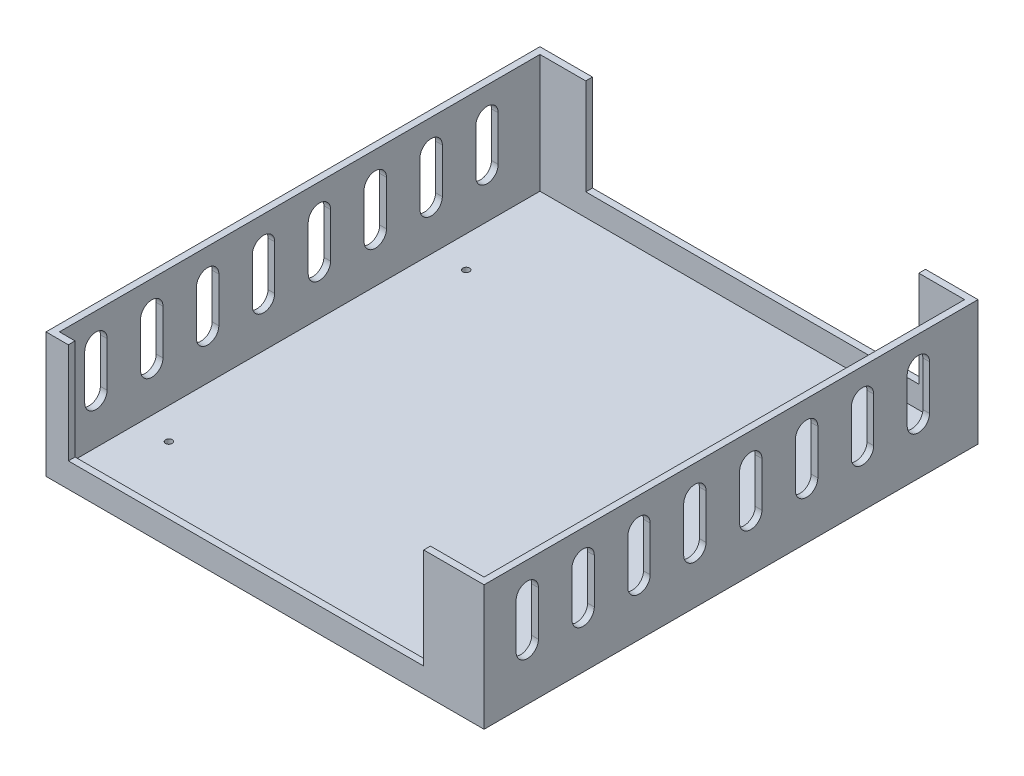
SolidWorks part; units mm, degrees
ref_plane "前视基准面" through (0, 0, 0) normal (0, 0, 1) x (1, 0, 0)
ref_plane "上视基准面" through (0, 0, 0) normal (0, 1, 0) x (1, 0, 0)
ref_plane "右视基准面" through (0, 0, 0) normal (1, 0, 0) x (0, 0, -1)
sketch "草图1" plane through (0, 0, 0) normal (0, 1, 0) x (1, 0, 0)
  line L0 (0, 0) -> (190, 0)
  line L1 (0, 0) -> (0, 215)
  line L2 (0, 215) -> (190, 215)
  line L3 (190, 215) -> (190, 0)
  line L4 (190, 0) -> (190, 11)
  line L5 (-3, -3) -> (193, -3)
  line L6 (-3, -3) -> (-3, 218)
  line L7 (-3, 218) -> (193, 218)
  line L8 (193, 218) -> (193, -3)
  circle A4 centre (14, 168) radius 1.5
  circle A5 centre (173, 168) radius 1.5
  circle A6 centre (173, 11) radius 1.5
  circle A7 centre (14, 35) radius 1.5
  dimension "D1" = 3
ref_plane "基准面1" through (0, -3, 0) normal (0, 1, 0) x (1, 0, 0)
sketch "草图2" plane through (0, -3, 0) normal (0, 1, 0) x (1, 0, 0)
  line L0 (-3, 218) -> (193, 218)
  line L1 (193, 218) -> (193, -3)
  line L2 (193, -3) -> (-3, -3)
  line L3 (-3, -3) -> (-3, 218)
  circle A0 centre (14, 168) radius 1.5
  circle A1 centre (173, 168) radius 1.5
  circle A2 centre (173, 11) radius 1.5
  circle A3 centre (14, 35) radius 1.5
extrude "凸台-拉伸8" add sketch "草图2" along normal blind 3
extrude "凸台-拉伸9" add sketch "草图1" along normal blind 8 contours L5 L8 L7 L6 | L0 L1 L2 L3
ref_plane "基准面2" through (0, 8, 0) normal (0, 1, 0) x (1, 0, 0)
sketch "草图8" plane through (0, 8, 0) normal (0, 1, 0) x (1, 0, 0)
  line L0 (190, 0) -> (166, 0)
  line L1 (0, 0) -> (190, 0) construction
  line L2 (166, 0) -> (166, -3)
  line L3 (-3, -3) -> (193, -3) construction
  line L4 (166, -3) -> (193, -3)
  line L5 (193, -3) -> (193, 218)
  line L6 (193, 218) -> (-3, 218)
  line L7 (-3, 218) -> (-3, -3)
  line L8 (166, 0) -> (190, 0)
  line L9 (190, 215) -> (0, 215)
  line L10 (0, 215) -> (0, 0)
  line L11 (166, -3) -> (193, -3)
  line L12 (193, 218) -> (-3, 218)
  line L14 (7, -3) -> (7, 0)
  line L15 (7, 0) -> (0, 0)
  line L16 (0, 215) -> (190, 215)
  line L17 (190, 0) -> (166, 0)
  line L18 (166, -3) -> (193, -3)
ref_plane "基准面3" through (0, 8, 0) normal (0, 1, 0) x (1, 0, 0)
sketch "草图9" plane through (0, 8, 0) normal (0, 1, 0) x (1, 0, 0)
  line L0 (166, -3) -> (193, -3)
  line L1 (193, -3) -> (193, 218)
  line L2 (193, 218) -> (-3, 218)
  line L3 (-3, 218) -> (-3, -3)
  line L4 (-3, -3) -> (7, -3)
  line L5 (7, -3) -> (7, 0)
  line L6 (7, 0) -> (0, 0)
  line L7 (0, 0) -> (0, 215)
  line L8 (0, 215) -> (190, 215)
  line L9 (190, 215) -> (190, 0)
  line L10 (190, 0) -> (166, 0)
  line L11 (166, 0) -> (166, -3)
extrude "凸台-拉伸10" add sketch "草图9" along normal blind 45
ref_plane "基准面4" through (0, 0, -218) normal (0, 0, -1) x (-1, 0, 0)
sketch "草图10" plane through (0, 0, -218) normal (0, 0, -1) x (-1, 0, 0)
  line L3 (-95, 10) -> (-169.5, 10)
  line L4 (-169.5, 10) -> (-169.5, 53)
  line L5 (-169.5, 53) -> (-20.5, 53)
  line L6 (-20.5, 53) -> (-20.5, 10)
  line L7 (-20.5, 10) -> (-95, 10)
extrude "切除-拉伸1" cut sketch "草图10" against normal blind 5 contours L4 L5 L6 L7 L3
ref_plane "基准面5" through (193, 0, 0) normal (1, 0, 0) x (0, 0, -1)
sketch "草图11" plane through (193, 0, 0) normal (1, 0, 0) x (0, 0, -1)
  line L15 (196.3269, 39.7408) -> (196.3269, 19.7408)
  line L16 (36.3269, 39.7408) -> (36.3269, 19.7408)
  line L17 (11.3269, 39.7408) -> (11.3269, 19.7408)
  line L18 (21.3269, 39.7408) -> (21.3269, 19.7408)
  line L20 (46.3269, 19.7408) -> (46.3269, 39.7408)
  line L21 (61.3269, 39.7408) -> (61.3269, 19.7408)
  line L23 (71.3269, 19.7408) -> (71.3269, 39.7408)
  line L24 (86.3269, 39.7408) -> (86.3269, 19.7408)
  line L26 (96.3269, 19.7408) -> (96.3269, 39.7408)
  line L27 (111.3269, 39.7408) -> (111.3269, 19.7408)
  line L29 (121.3269, 19.7408) -> (121.3269, 39.7408)
  line L30 (136.3269, 39.7408) -> (136.3269, 19.7408)
  line L32 (146.3269, 19.7408) -> (146.3269, 39.7408)
  line L33 (161.3269, 39.7408) -> (161.3269, 19.7408)
  line L35 (171.3269, 19.7408) -> (171.3269, 39.7408)
  line L36 (186.3269, 39.7408) -> (186.3269, 19.7408)
  arc A0 (41.3269, 14.7408) -> (36.3269, 19.7408) centre (41.3269, 19.7408) cw
  arc A1 (16.3269, 14.7408) -> (11.3269, 19.7408) centre (16.3269, 19.7408) cw
  arc A2 (61.3269, 39.7408) -> (66.3269, 44.7408) centre (66.3269, 39.7408) cw
  arc A3 (86.3269, 39.7408) -> (91.3269, 44.7408) centre (91.3269, 39.7408) cw
  arc A4 (111.3269, 39.7408) -> (116.3269, 44.7408) centre (116.3269, 39.7408) cw
  arc A5 (136.3269, 39.7408) -> (141.3269, 44.7408) centre (141.3269, 39.7408) cw
  arc A6 (161.3269, 39.7408) -> (166.3269, 44.7408) centre (166.3269, 39.7408) cw
  arc A7 (186.3269, 39.7408) -> (191.3269, 44.7408) centre (191.3269, 39.7408) cw
  arc A8 (36.3269, 39.7408) -> (41.3269, 44.7408) centre (41.3269, 39.7408) cw
  arc A9 (11.3269, 39.7408) -> (16.3269, 44.7408) centre (16.3269, 39.7408) cw
  arc A10 (191.3269, 14.7408) -> (186.3269, 19.7408) centre (191.3269, 19.7408) cw
  arc A11 (166.3269, 14.7408) -> (161.3269, 19.7408) centre (166.3269, 19.7408) cw
  arc A12 (141.3269, 14.7408) -> (136.3269, 19.7408) centre (141.3269, 19.7408) cw
  arc A13 (116.3269, 14.7408) -> (111.3269, 19.7408) centre (116.3269, 19.7408) cw
  arc A14 (91.3269, 14.7408) -> (86.3269, 19.7408) centre (91.3269, 19.7408) cw
  arc A15 (66.3269, 14.7408) -> (61.3269, 19.7408) centre (66.3269, 19.7408) cw
  arc A16 (21.3269, 39.7408) -> (16.3269, 44.7408) centre (16.3269, 39.7408) ccw
  arc A17 (46.3269, 39.7408) -> (41.3269, 44.7408) centre (41.3269, 39.7408) ccw
  arc A18 (71.3269, 39.7408) -> (66.3269, 44.7408) centre (66.3269, 39.7408) ccw
  arc A19 (96.3269, 39.7408) -> (91.3269, 44.7408) centre (91.3269, 39.7408) ccw
  arc A20 (121.3269, 39.7408) -> (116.3269, 44.7408) centre (116.3269, 39.7408) ccw
  arc A21 (146.3269, 39.7408) -> (141.3269, 44.7408) centre (141.3269, 39.7408) ccw
  arc A22 (171.3269, 39.7408) -> (166.3269, 44.7408) centre (166.3269, 39.7408) ccw
  arc A23 (196.3269, 39.7408) -> (191.3269, 44.7408) centre (191.3269, 39.7408) ccw
  arc A24 (16.3269, 14.7408) -> (21.3269, 19.7408) centre (16.3269, 19.7408) ccw
  arc A25 (41.3269, 14.7408) -> (46.3269, 19.7408) centre (41.3269, 19.7408) ccw
  arc A26 (66.3269, 14.7408) -> (71.3269, 19.7408) centre (66.3269, 19.7408) ccw
  arc A27 (91.3269, 14.7408) -> (96.3269, 19.7408) centre (91.3269, 19.7408) ccw
  arc A28 (116.3269, 14.7408) -> (121.3269, 19.7408) centre (116.3269, 19.7408) ccw
  arc A29 (141.3269, 14.7408) -> (146.3269, 19.7408) centre (141.3269, 19.7408) ccw
  arc A30 (166.3269, 14.7408) -> (171.3269, 19.7408) centre (166.3269, 19.7408) ccw
  arc A31 (191.3269, 14.7408) -> (196.3269, 19.7408) centre (191.3269, 19.7408) ccw
  dimension "D1" = 5
  dimension "D2" = 5
  dimension "D3" = 5
  dimension "D4" = 5
  dimension "D5" = 5
  dimension "D6" = 5
  dimension "D7" = 5
  dimension "D8" = 5
  dimension "D9" = 5
extrude "切除-拉伸2" cut sketch "草图11" against normal blind 209
